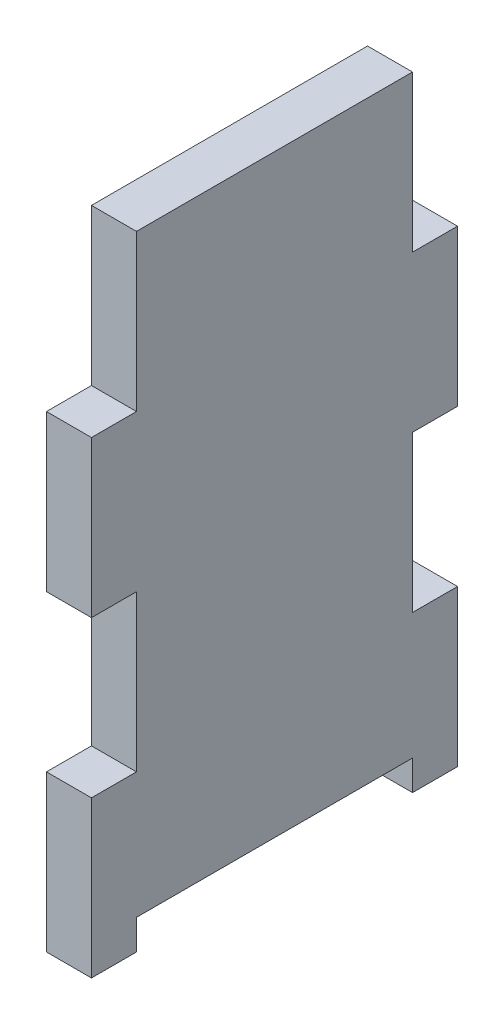
SolidWorks part; units mm, degrees
ref_plane "Front Plane" through (0, 0, 0) normal (0, 0, 1) x (1, 0, 0)
ref_plane "Top Plane" through (0, 0, 0) normal (0, 1, 0) x (1, 0, 0)
ref_plane "Right Plane" through (0, 0, 0) normal (1, 0, 0) x (0, 0, -1)
sketch "Sketch1" plane through (0, 0, 0) normal (1, 0, 0) x (0, 0, -1)
  line L0 (0, -99.06) -> (9.525, -99.06)
  line L1 (0, 0) -> (77.47, 0)
  line L2 (0, 0) -> (0, -132.08)
  line L3 (0, -132.08) -> (77.47, -132.08)
  line L4 (77.47, 0) -> (77.47, -132.08)
  line L5 (9.525, -99.06) -> (9.525, -66.04)
  line L6 (9.525, -66.04) -> (0, -66.04)
  line L7 (9.525, 0) -> (9.525, -33.02)
  line L8 (9.525, -33.02) -> (0, -33.02)
  line L9 (38.735, 0) -> (38.735, -132.08) construction
  line L10 (77.47, -99.06) -> (67.945, -99.06)
  line L11 (67.945, -99.06) -> (67.945, -66.04)
  line L12 (67.945, -66.04) -> (77.47, -66.04)
  line L13 (67.945, -33.02) -> (77.47, -33.02)
  line L14 (67.945, 0) -> (67.945, -33.02)
  dimension "D1" = 77.47
  dimension "D2" = 132.08
  dimension "D3" = 33.02
  dimension "D4" = 33.02
  dimension "D5" = 9.525
  dimension "D6" = 9.525
  dimension "D7" = 33.02
extrude "Boss-Extrude1" add sketch "Sketch1" along normal blind 9.525 contours L1 L9 L3 L4 L10 L11 L12 L13 L14 | L9 L1 L7 L8 L2 L6 L5 L0 L3
sketch "Sketch2" plane through (9.525, 0, 0) normal (1, 0, 0) x (0, 0, -1)
  line L0 (0, -132.08) -> (77.47, -132.08) construction
  line L1 (9.525, -132.08) -> (67.945, -132.08)
  line L2 (9.525, -132.08) -> (9.525, -125.73)
  line L3 (9.525, -125.73) -> (67.945, -125.73)
  line L4 (67.945, -132.08) -> (67.945, -125.73)
  line L5 (9.525, -99.06) -> (9.525, -66.04) construction
  line L6 (67.945, -99.06) -> (67.945, -66.04) construction
  dimension "D1" = 6.35
extrude "Cut-Extrude1" cut sketch "Sketch2" against normal blind 46.99
